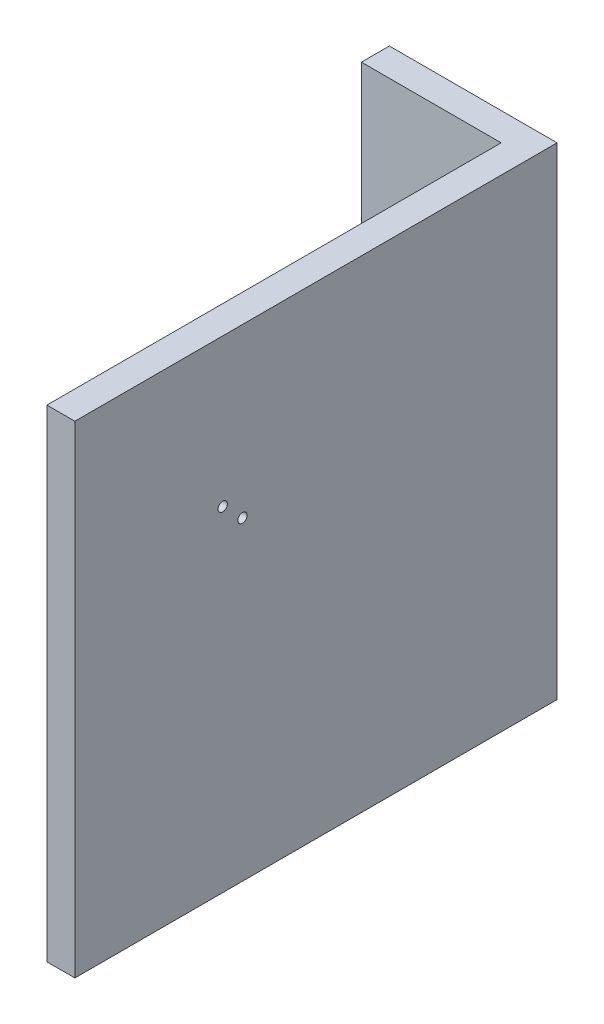
SolidWorks part; units mm, degrees
ref_plane "Plano frontal" through (0, 0, 0) normal (0, 0, 1) x (1, 0, 0)
ref_plane "Plano superior" through (0, 0, 0) normal (0, 1, 0) x (1, 0, 0)
ref_plane "Plano direito" through (0, 0, 0) normal (1, 0, 0) x (0, 0, -1)
sketch "Sketch1" plane through (-23098.6126, 0, 0) normal (-1, 0, 0) x (0, 0, 1)
  line L1 (40951.905, 7024.3016) -> (40606.9075, 7024.3016)
  line L2 (40951.905, 7024.3016) -> (40951.905, 6679.3041)
  line L3 (40951.905, 6679.3041) -> (40606.9075, 6679.3041)
  line L4 (40606.9075, 7024.3016) -> (40606.9075, 6679.3041)
  point P4 (40354.1742, 5720.2569)
extrude "Boss-Extrude1" add sketch "Sketch1" along normal blind 20
sketch "Sketch2" plane through (-23118.6126, 0, 0) normal (-1, 0, 0) x (0, 0, 1)
  circle A0 centre (40846.136, 6918.5326) radius 3.35
  circle A1 centre (40831.9939, 6904.3905) radius 3.35
  circle A2 centre (40846.136, 6918.5326) radius 3.35 construction
  circle A3 centre (40831.9939, 6904.3905) radius 3.35 construction
  point P4 (0, 0)
extrude "Cut-Extrude1" cut sketch "Sketch2" against normal through all
sketch "Sketch3" plane through (-23118.6126, 0, 0) normal (-1, 0, 0) x (0, 0, 1)
  line L0 (40606.9075, 6679.3041) -> (40951.905, 6679.3041) construction
  line L1 (40606.9075, 7024.3016) -> (40626.9075, 7024.3016)
  line L2 (40606.9075, 7024.3016) -> (40606.9075, 6679.3041)
  line L3 (40606.9075, 6679.3041) -> (40626.9075, 6679.3041)
  line L4 (40626.9075, 7024.3016) -> (40626.9075, 6679.3041)
  dimension "D1" = 20
extrude "Boss-Extrude2" add sketch "Sketch3" along normal blind 100
